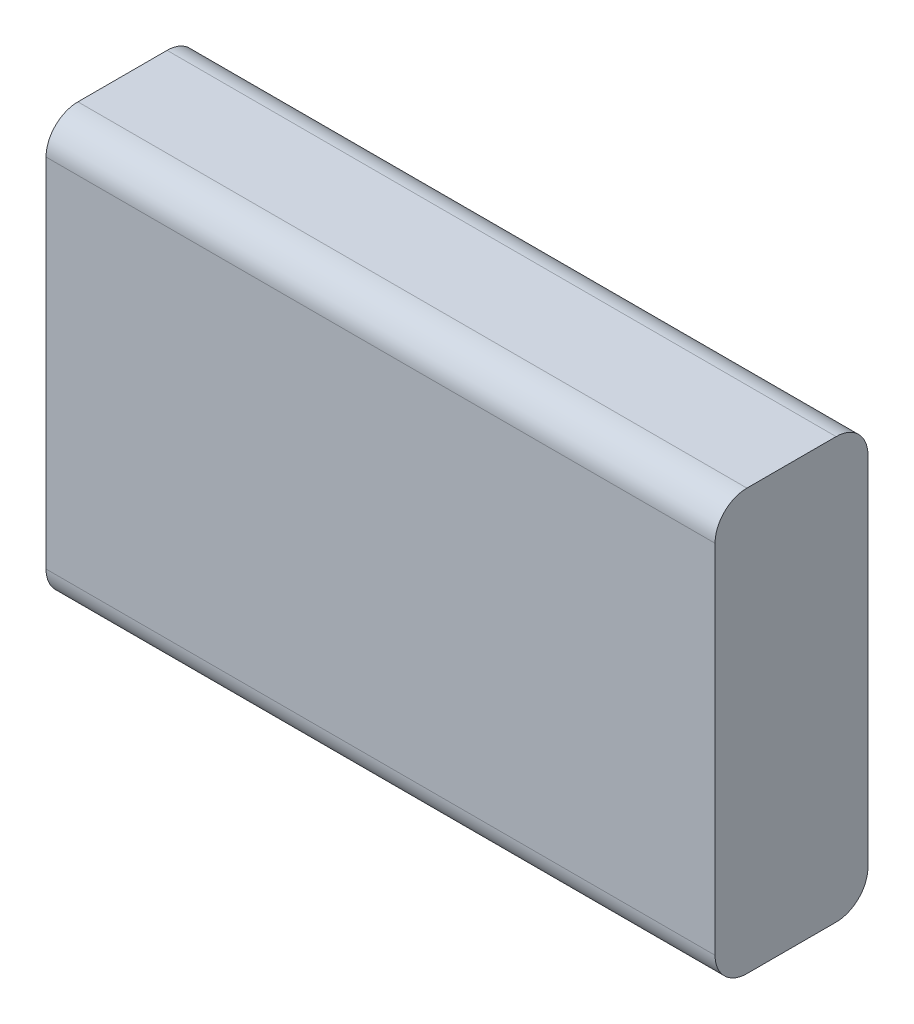
SolidWorks part; units mm, degrees
ref_plane "Front Plane" through (0, 0, 0) normal (0, 0, 1) x (1, 0, 0)
ref_plane "Top Plane" through (0, 0, 0) normal (0, 1, 0) x (1, 0, 0)
ref_plane "Right Plane" through (0, 0, 0) normal (1, 0, 0) x (0, 0, -1)
sketch "Sketch1" plane through (0, 0, 0) normal (0, 0, 1) x (1, 0, 0)
  line L1 (-5.0868, 64.3242) -> (99.9132, 64.3242)
  line L2 (-5.0868, 64.3242) -> (-5.0868, -1.6758)
  line L3 (-5.0868, -1.6758) -> (99.9132, -1.6758)
  line L4 (99.9132, 64.3242) -> (99.9132, -1.6758)
  dimension "D1" = 105
  dimension "D2" = 66
extrude "Boss-Extrude1" add sketch "Sketch1" along normal blind 24
fillet "Fillet1" radius 5 4 edges at (47.4132, -1.6758, 0) (47.4132, -1.6758, 24) (47.4132, 64.3242, 0) (47.4132, 64.3242, 24)
